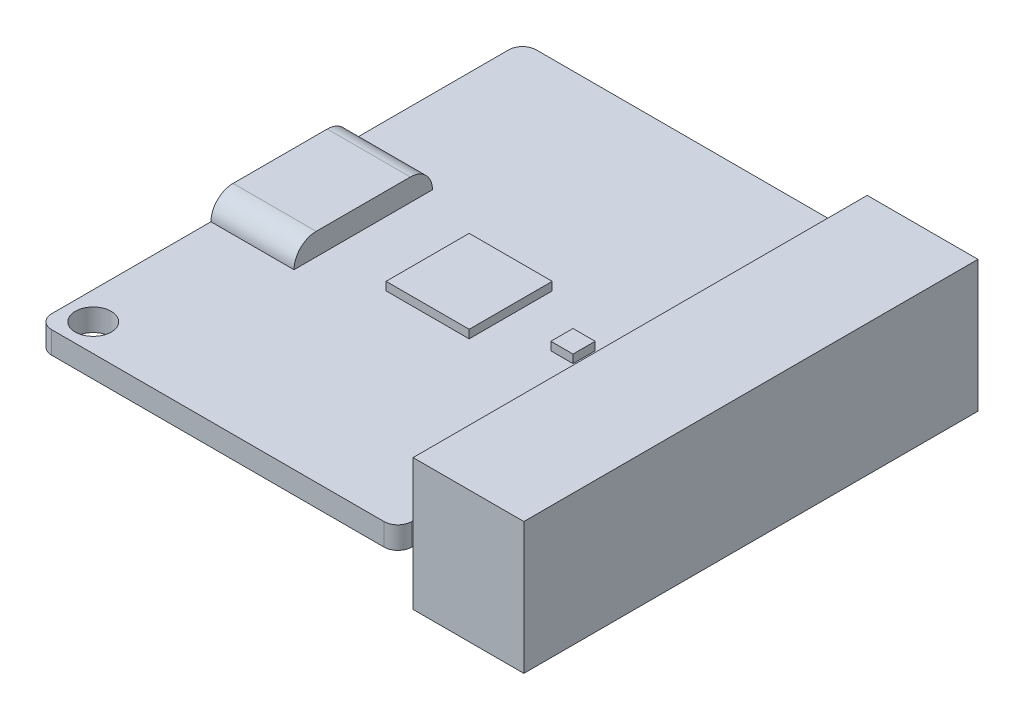
SolidWorks part; units mm, degrees
ref_plane "前视基准面" through (0, 0, 0) normal (0, 0, 1) x (1, 0, 0)
ref_plane "上视基准面" through (0, 0, 0) normal (0, 1, 0) x (1, 0, 0)
ref_plane "右视基准面" through (0, 0, 0) normal (1, 0, 0) x (0, 0, -1)
sketch "草图1" plane through (0, 0, 0) normal (0, 1, 0) x (1, 0, 0)
  line L1 (-12, -17.5) -> (12, -17.5)
  line L2 (-13, -16.5) -> (-13, 16.5)
  line L3 (-12, 17.5) -> (12, 17.5)
  line L4 (13, -16.5) -> (13, 16.5)
  line L5 (-13, -17.5) -> (13, 17.5) construction
  line L6 (-13, 17.5) -> (13, -17.5) construction
  arc A0 (-13, 16.5) -> (-12, 17.5) centre (-12, 16.5) cw
  arc A1 (12, 17.5) -> (13, 16.5) centre (12, 16.5) cw
  arc A2 (12, -17.5) -> (13, -16.5) centre (12, -16.5) ccw
  arc A3 (-12, -17.5) -> (-13, -16.5) centre (-12, -16.5) cw
  circle A4 centre (-11, -15.5) radius 1.3
  circle A5 centre (11, 15.5) radius 1.3
  point P0 (0, 0)
  dimension "D3" = 1
  dimension "D4" = 2.6
  dimension "D5" = 2
  dimension "D6" = 2
  dimension "D7" = 2
  dimension "D8" = 2
  dimension "D1" = 26
  dimension "D2" = 35
extrude "凸台-拉伸1" add sketch "草图1" along normal blind 1.6
sketch "草图2" plane through (-13, 0, 0) normal (-1, 0, 0) x (0, 0, 1)
  line L0 (-3.4, 1.6) -> (3.4, 1.6) construction
  line L1 (-16.5, 1.6) -> (16.5, 1.6) construction
  line L2 (-3.4, 3.2) -> (3.4, 3.2)
  line L3 (-3.4, 0) -> (3.4, 0)
  line L4 (-3.4, 3.2) -> (3.4, 0) construction
  line L6 (-16.5, 0) -> (16.5, 0) construction
  arc A0 (-3.4, 3.2) -> (-3.4, 0) centre (-3.4, 1.6) ccw
  arc A1 (3.4, 0) -> (3.4, 3.2) centre (3.4, 1.6) ccw
  point P4 (0, 1.6)
  point P11 (0, 0)
  point P12 (-5, 1.6)
  point P13 (5, 1.6)
  point P16 (0, 1.6)
  dimension "D1" = 10
extrude "凸台-拉伸2" add sketch "草图2" against normal blind 6
sketch "草图3" plane through (0, 1.6, 0) normal (0, 1, 0) x (1, 0, 0)
  line L0 (-12, -17.5) -> (12, -17.5) construction
  line L1 (3.65, 3) -> (-2.35, 3)
  line L2 (3.65, 3) -> (3.65, -3)
  line L3 (3.65, -3) -> (-2.35, -3)
  line L4 (-2.35, 3) -> (-2.35, -3)
  line L5 (3.65, 3) -> (-2.35, -3) construction
  line L6 (3.65, -3) -> (-2.35, 3) construction
  line L7 (-13, 16.5) -> (-13, 5) construction
  point P0 (0.65, 0)
  dimension "D1" = 17.5
  dimension "D2" = 13.65
  dimension "D3" = 6
  dimension "D4" = 6
extrude "凸台-拉伸3" add sketch "草图3" along normal blind 0.6
sketch "草图4" plane through (0, 1.6, 0) normal (0, 1, 0) x (1, 0, 0)
  line L0 (3.65, -3) -> (-2.35, 3) construction
  line L1 (8.95, 0.8) -> (7.35, 0.8)
  line L2 (8.95, 0.8) -> (8.95, -0.8)
  line L3 (8.95, -0.8) -> (7.35, -0.8)
  line L4 (7.35, 0.8) -> (7.35, -0.8)
  line L5 (8.95, 0.8) -> (7.35, -0.8) construction
  line L6 (8.95, -0.8) -> (7.35, 0.8) construction
  point P0 (8.15, 0)
  point P9 (0, 0)
  point P14 (0.65, 0)
  dimension "D1" = 7.5
  dimension "D2" = 1.6
  dimension "D3" = 1.6
extrude "凸台-拉伸4" add sketch "草图4" along normal blind 0.6
sketch "草图5" plane through (13, 0, 0) normal (1, 0, 0) x (0, 0, -1)
  line L0 (-17.5, 1.6) -> (17.5, 0) construction
  line L1 (-16.4, -3.95) -> (16.4, -3.95)
  line L2 (-16.4, -3.95) -> (-16.4, 5.55)
  line L3 (-16.4, 5.55) -> (16.4, 5.55)
  line L4 (16.4, -3.95) -> (16.4, 5.55)
  line L5 (-16.4, -3.95) -> (16.4, 5.55) construction
  line L6 (-16.4, 5.55) -> (16.4, -3.95) construction
  point P0 (0, 0.8)
  point P9 (0, 0.8)
  dimension "D1" = 32.8
  dimension "D2" = 9.5
extrude "凸台-拉伸5" add sketch "草图5" along normal blind 8
